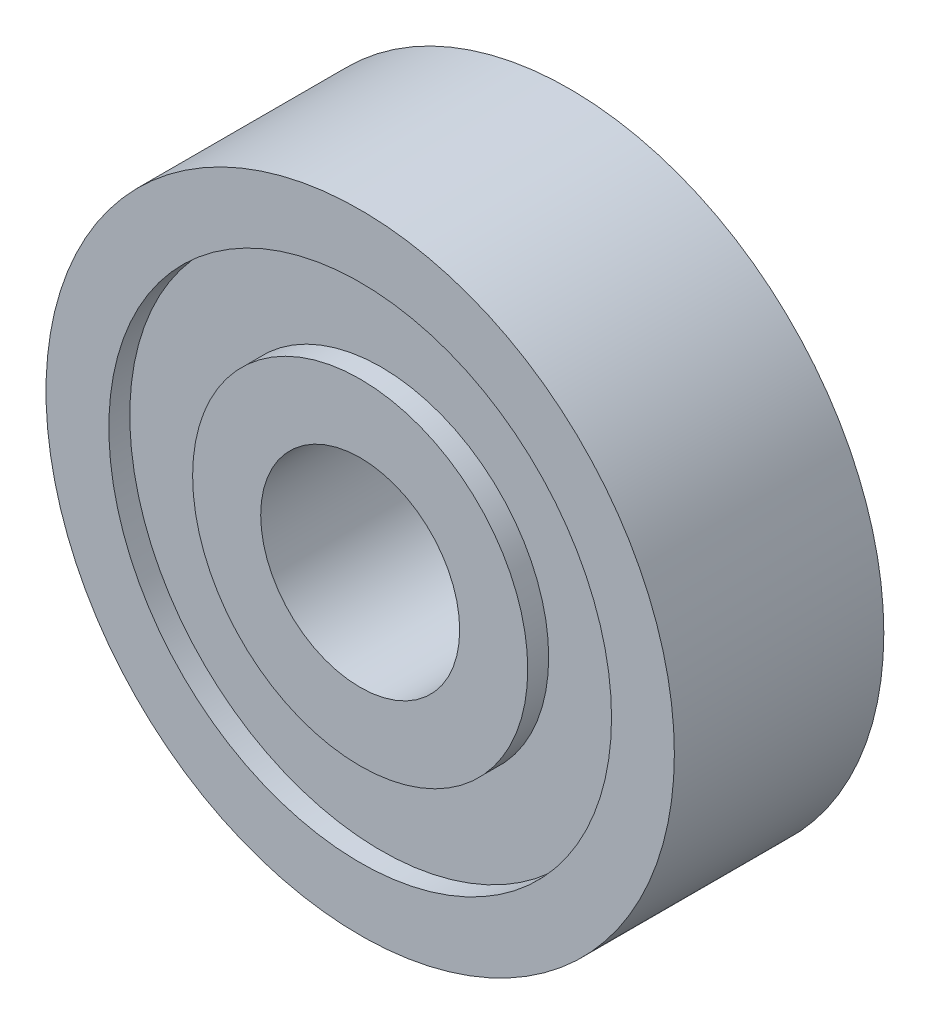
SolidWorks part; units mm, degrees
ref_plane "Front Plane" through (0, 0, 0) normal (0, 0, 1) x (1, 0, 0)
ref_plane "Top Plane" through (0, 0, 0) normal (0, 1, 0) x (1, 0, 0)
ref_plane "Right Plane" through (0, 0, 0) normal (1, 0, 0) x (0, 0, -1)
sketch "Sketch1" plane through (0, 0, 0) normal (0, 0, 1) x (1, 0, 0)
  circle A0 centre (0, 0) radius 4.75
  circle A1 centre (0, 0) radius 15
extrude "Boss-Extrude1" add sketch "Sketch1" along normal blind 10
sketch "Sketch2" plane through (0, 0, 0) normal (0, 0, 1) x (1, 0, 0)
  circle A0 centre (0, 0) radius 8
  circle A1 centre (0, 0) radius 12
extrude "Cut-Extrude1" cut sketch "Sketch2" along normal blind 1
ref_plane "Plane2" through (0, 0, 10) normal (0, 0, 1) x (1, 0, 0)
sketch "Sketch4" plane through (0, 0, 10) normal (0, 0, 1) x (1, 0, 0)
  circle A0 centre (0, 0) radius 8
  circle A1 centre (0, 0) radius 12
extrude "Cut-Extrude2" cut sketch "Sketch4" against normal blind 1
